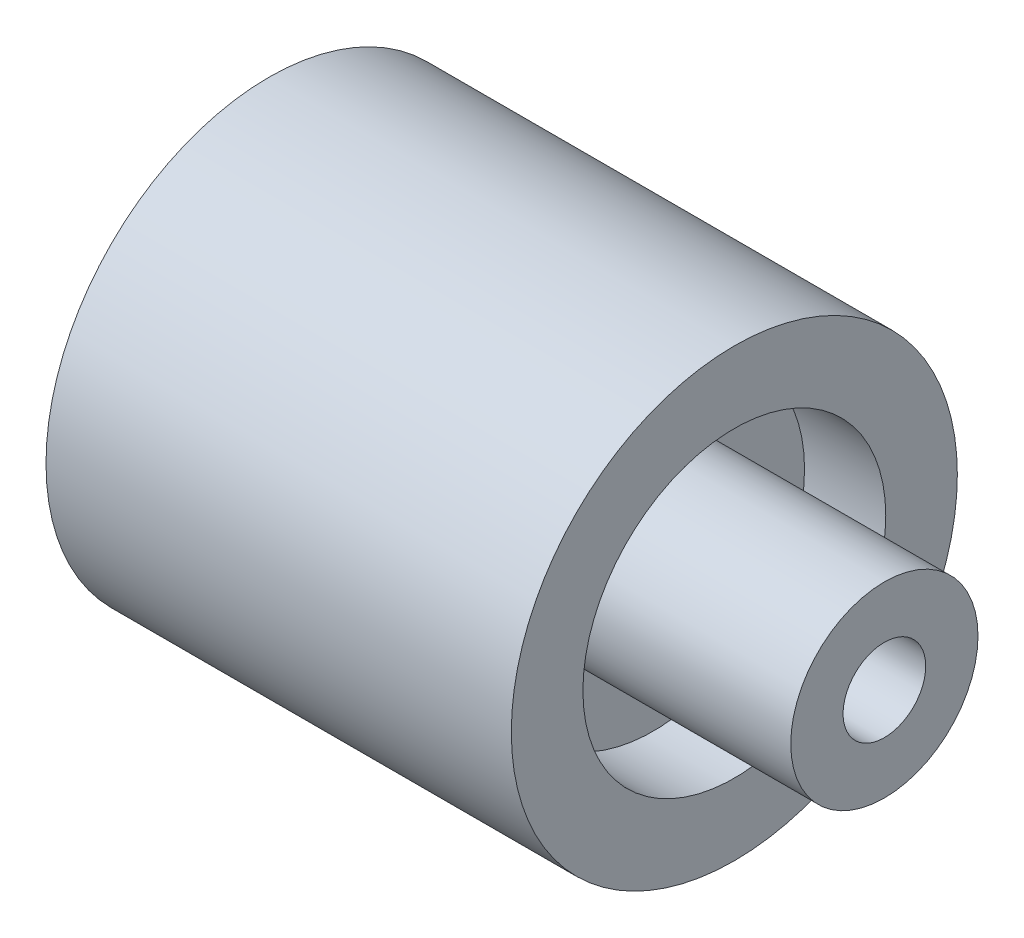
SolidWorks part; units mm, degrees
ref_plane "正面" through (0, 0, 0) normal (0, 0, 1) x (1, 0, 0)
ref_plane "平面" through (0, 0, 0) normal (0, 1, 0) x (1, 0, 0)
ref_plane "右側面" through (0, 0, 0) normal (1, 0, 0) x (0, 0, -1)
sketch "ｽｹｯﾁ1" plane through (0, 0, 0) normal (1, 0, 0) x (0, 0, -1)
  circle A0 centre (0, 0) radius 5.5
  dimension "D1" = 11
extrude "ﾎﾞｽ - 押し出し1" add sketch "ｽｹｯﾁ1" along normal blind 11 contours A0
sketch "ｽｹｯﾁ2" plane through (11, 0, 0) normal (1, 0, 0) x (0, 0, -1)
  circle A0 centre (0, 0) radius 2.7
  circle A1 centre (0, 0) radius 5.5 construction
  dimension "D1" = 2.8
extrude "ｶｯﾄ - 押し出し1" cut sketch "ｽｹｯﾁ2" against normal blind 9.35
sketch "ｽｹｯﾁ4" plane through (1.65, 0, 0) normal (1, 0, 0) x (0, 0, -1)
  circle A0 centre (0, 0) radius 3.4
  dimension "D1" = 6.8
extrude "ﾎﾞｽ - 押し出し2" add sketch "ｽｹｯﾁ4" along normal blind 17.75
sketch "ｽｹｯﾁ5" plane through (19.4, 0, 0) normal (1, 0, 0) x (0, 0, -1)
  circle A0 centre (0, 0) radius 1.5
  dimension "D1" = 3
extrude "ｶｯﾄ - 押し出し4" cut sketch "ｽｹｯﾁ5" against normal blind 25.75
sketch "ｽｹｯﾁ6" plane through (0, 0, 0) normal (-1, 0, 0) x (0, 0, 1)
  circle A0 centre (0, 0) radius 8.1
  circle A1 centre (0, 0) radius 5.5
  dimension "D1" = 16.2
  dimension "D2" = 11
extrude "ﾎﾞｽ - 押し出し4" add sketch "ｽｹｯﾁ6" against normal blind 13.95 and the other way blind 2.95
